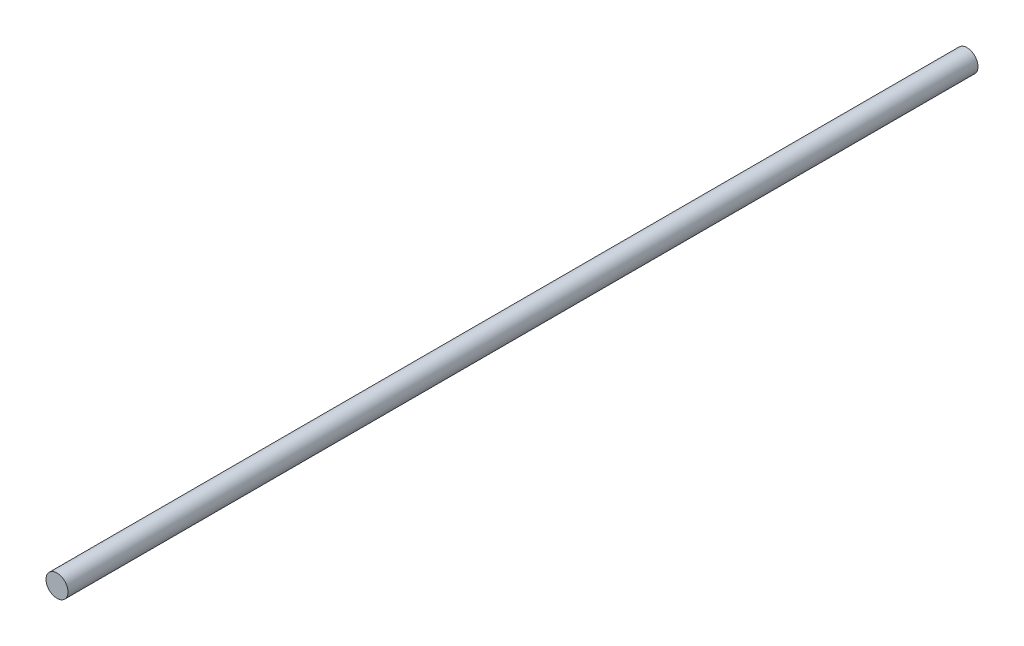
SolidWorks part; units mm, degrees
ref_plane "Front" through (0, 0, 0) normal (0, 0, 1) x (1, 0, 0)
ref_plane "Top" through (0, 0, 0) normal (0, 1, 0) x (1, 0, 0)
ref_plane "Right" through (0, 0, 0) normal (1, 0, 0) x (0, 0, -1)
sketch "Sketch1" plane through (0, 0, 0) normal (0, 0, 1) x (1, 0, 0)
  circle A0 centre (0, 0) radius 4
  dimension "D1" = 8
extrude "Boss-Extrude1" add sketch "Sketch1" along normal blind 331
equation "\"baseplate-height\" = 360mm"
equation "\"material-thickness\" = 9mm"
equation "\"linear-bar-dia\" = 8mm ' Diameter of the metal slide bar used on the X Axis"
equation "\"D1@Boss-Extrude1\"=\"baseplate-height\" - ( \"material-thickness\" +20 )"
equation "\"D1@Sketch1\" = \"linear-bar-dia\""
